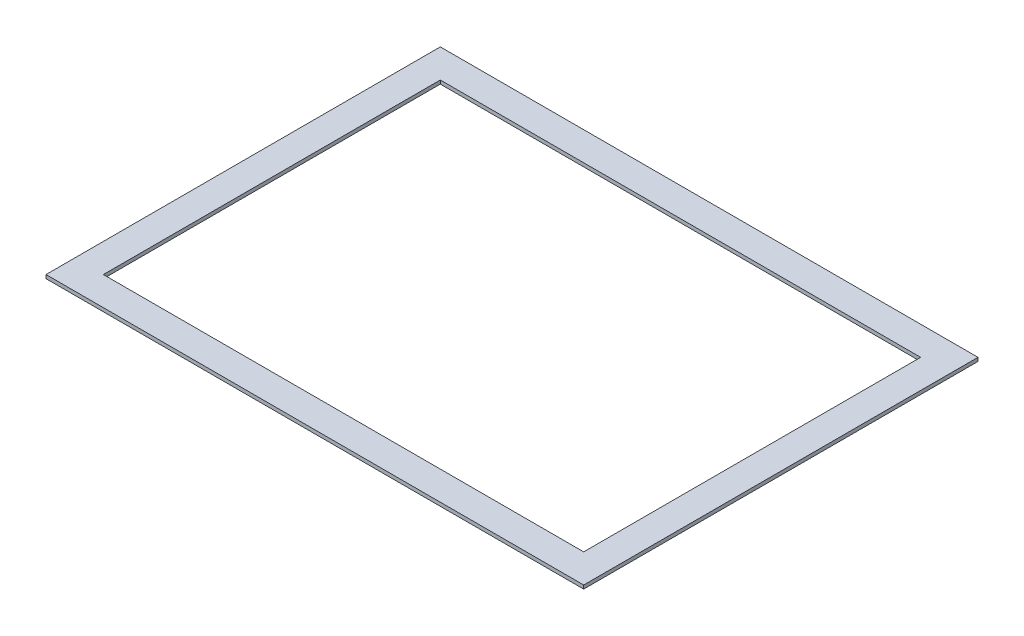
SolidWorks part; units mm, degrees
material "Silicon Rubber"
ref_plane "Front Plane" through (0, 0, 0) normal (0, 0, 1) x (1, 0, 0)
ref_plane "Top Plane" through (0, 0, 0) normal (0, 1, 0) x (1, 0, 0)
ref_plane "Right Plane" through (0, 0, 0) normal (1, 0, 0) x (0, 0, -1)
sketch "Sketch1" plane through (0, 0, 0) normal (0, 1, 0) x (1, 0, 0)
  line L0 (-212.725, 149.225) -> (212.725, 149.225)
  line L1 (-238.125, -174.625) -> (238.125, -174.625)
  line L2 (-238.125, -174.625) -> (-238.125, 174.625)
  line L3 (-238.125, 174.625) -> (238.125, 174.625)
  line L4 (238.125, -174.625) -> (238.125, 174.625)
  line L5 (-238.125, -174.625) -> (238.125, 174.625) construction
  line L6 (-238.125, 174.625) -> (238.125, -174.625) construction
  line L7 (212.725, -149.225) -> (212.725, 149.225)
  line L8 (-212.725, -149.225) -> (212.725, -149.225)
  line L9 (-212.725, -149.225) -> (-212.725, 149.225)
  point P0 (0, 0)
  dimension "D1" = 349.25
  dimension "D2" = 476.25
  dimension "D3" = 25.4
extrude "Boss-Extrude1" add sketch "Sketch1" along normal blind 3.175
